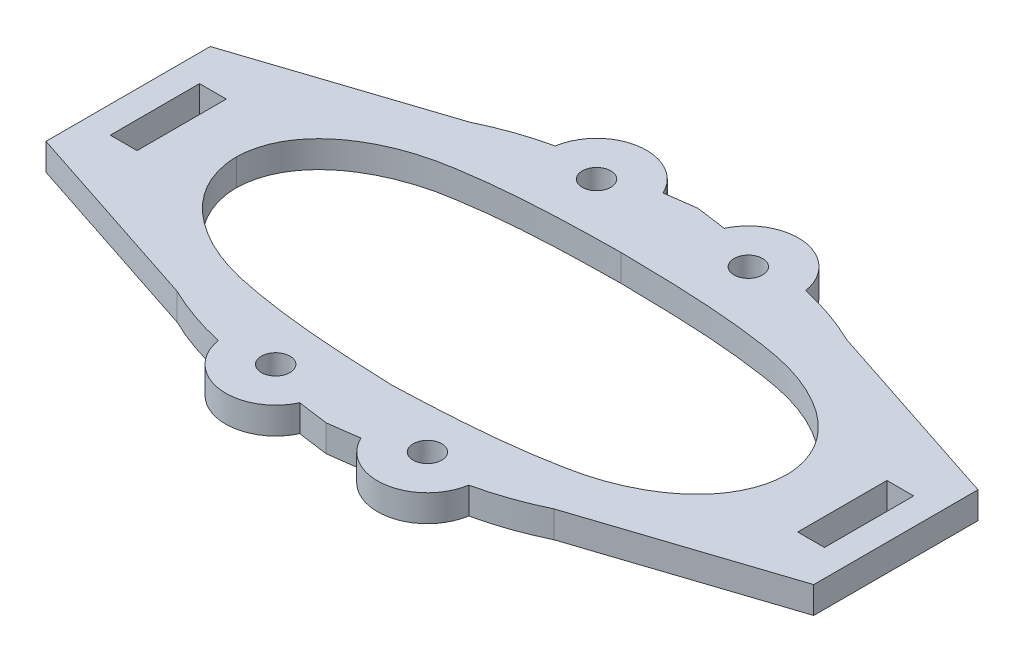
SolidWorks part; units mm, degrees
ref_plane "Plano frontal" through (0, 0, 0) normal (0, 0, 1) x (1, 0, 0)
ref_plane "Plano superior" through (0, 0, 0) normal (0, 1, 0) x (1, 0, 0)
ref_plane "Plano direito" through (0, 0, 0) normal (1, 0, 0) x (0, 0, -1)
ref_plane "Plano1" through (0, 10, 0) normal (0, -1, 0) x (1, 0, 0)
sketch "Esboço1" plane through (0, 10, 0) normal (0, -1, 0) x (1, 0, 0)
  line L0 (-40, 5) -> (-37, 5)
  line L1 (-37, 5) -> (-37, -5)
  line L2 (-37, -5) -> (-40, -5)
  line L3 (-40, -5) -> (-40, 5)
  line L4 (43, -9.1999) -> (21.1106, -16.3994)
  line L5 (43, 9.1999) -> (43, -9.1999)
  line L6 (21.1115, 16.4024) -> (43, 9.1999)
  line L7 (40, -5) -> (40, 5)
  line L9 (-21.1115, 16.4024) -> (-43, 9.1999)
  line L10 (-43, 9.1999) -> (-43, -9.1999)
  line L11 (-43, -9.1999) -> (-21.1106, -16.3994)
  line L14 (0, -20.8143) -> (0, 20.8143) construction
  line L15 (37, -5) -> (40, -5)
  line L16 (37, 5) -> (37, -5)
  line L17 (40, 5) -> (37, 5)
  circle A0 centre (-8.5, -17.9721) radius 1.6
  arc A1 (0, -20.8143) -> (3.4275, -20.3448) centre (-24.7518, 172.6059) ccw
  arc A2 (14.0273, -18.8715) -> (3.4275, -20.3448) centre (8.5, -17.9721) cw
  circle A3 centre (-8.5, 17.9721) radius 1.6
  arc A7 (-3.4275, 20.3448) -> (0, 20.8143) centre (25.2205, -176.0209) cw
  arc A8 (-3.4275, 20.3448) -> (-14.0273, 18.8715) centre (-8.5, 17.9721) ccw
  arc A9 (-21.1115, 16.4024) -> (-14.0273, 18.8715) centre (-6.9118, -12.9403) cw
  arc A10 (-14.0273, -18.8715) -> (-21.1106, -16.3994) centre (-7.0016, 12.6429) cw
  arc A11 (-14.0273, -18.8715) -> (-3.4275, -20.3448) centre (-8.5, -17.9721) ccw
  arc A12 (0, -20.8143) -> (-3.4275, -20.3448) centre (24.7518, 172.6059) cw
  arc A16 (14.0273, -18.8715) -> (21.1106, -16.3994) centre (7.0016, 12.6429) ccw
  arc A17 (21.1115, 16.4024) -> (14.0273, 18.8715) centre (6.9118, -12.9403) ccw
  arc A18 (3.4275, 20.3448) -> (14.0273, 18.8715) centre (8.5, 17.9721) cw
  arc A19 (3.4275, 20.3448) -> (0, 20.8143) centre (-25.2205, -176.0209) ccw
  circle A20 centre (8.5, 17.9721) radius 1.6
  circle A21 centre (8.5, -17.9721) radius 1.6
  spline S0 degree 3 poles (0, 13.4818) (-6.2258, 13.2439) (-12.4817, 12.9252) (-24.656, 10.3194) (-30.738, 6.2728) (-30.8333, 0) knots 0 0 0 0 0.5 0.5 1 1 1 1
  spline S1 degree 3 poles (30.8333, 0) (30.6647, -6.1693) (24.4065, -9.8499) (12.3094, -12.0029) (6.143, -12.1444) (0, -12.225) knots 0 0 0 0 0.5 0.5 1 1 1 1
  spline S2 degree 3 poles (0, 13.4818) (6.2258, 13.2439) (12.4817, 12.9252) (24.656, 10.3194) (30.738, 6.2728) (30.8333, 0) knots 0 0 0 0 0.5 0.5 1 1 1 1
  spline S3 degree 3 poles (-30.8333, 0) (-30.6647, -6.1693) (-24.4065, -9.8499) (-12.3094, -12.0029) (-6.143, -12.1444) (0, -12.225) knots 0 0 0 0 0.5 0.5 1 1 1 1
  dimension "D1" = 5.6
  dimension "D2" = 3.2
  dimension "D3" = 61.6667
  dimension "D4" = 32.2881
  dimension "D5" = 23.043
  dimension "D12" = 32.5979
  dimension "D13" = 5.6
  dimension "D14" = 3.2
  dimension "D15" = 25.7068
  dimension "D6" = 18.3998
  dimension "D7" = 23.043
  dimension "D8" = 3
  dimension "D9" = 10
  dimension "D10" = 3
  dimension "D11" = 4.1999
  dimension "D16" = 43
extrude "Ressalto-extrusão1" add sketch "Esboço1" against normal blind 3
